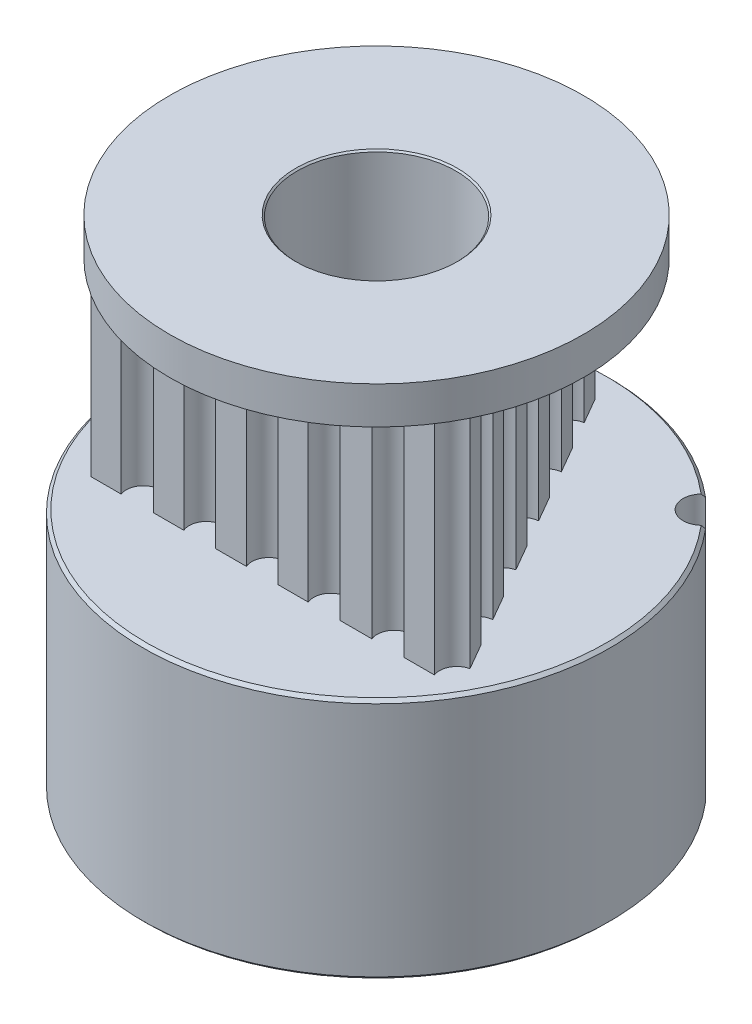
SolidWorks part; units mm, degrees
material "6061 slitina"
ref_plane "Přední rovina" through (0, 0, 0) normal (0, 0, 1) x (1, 0, 0)
ref_plane "Horní rovina" through (0, 0, 0) normal (0, 1, 0) x (1, 0, 0)
ref_plane "Pravá rovina" through (0, 0, 0) normal (1, 0, 0) x (0, 0, -1)
sketch "Skica1" plane through (0, 0, 0) normal (0, 1, 0) x (1, 0, 0)
  circle A0 centre (0, 0) radius 2.5
  arc B0 (-5.7301, 1.0983) -> (-5.3872, 2.2403) centre (-5.6803, 1.7058) ccw
  arc B1 (-5.7301, 1.0983) -> (-5.922, 1.0859) centre (-5.7841, 0.4401) ccw
  arc B2 (-5.922, 1.0859) -> (-6.0197, 1.0387) centre (-5.8743, 0.8624) ccw
  arc B3 (-6.0197, 1.0387) -> (-6.0791, 0.6004) centre (0, 0) ccw
  arc B4 (-6.0791, 0.6004) -> (-5.9974, 0.5289) centre (-5.892, 0.7317) ccw
  arc B5 (-5.9974, 0.5289) -> (-5.8158, 0.466) centre (-5.6927, 1.1148) ccw
  arc B6 (-5.7891, -0.7262) -> (-5.8158, 0.466) centre (-5.9294, -0.133) ccw
  arc B7 (-5.7891, -0.7262) -> (-5.9677, -0.7972) centre (-5.637, -1.3689) ccw
  arc B8 (-5.9677, -0.7972) -> (-6.0461, -0.8723) centre (-5.8532, -0.9951) ccw
  arc B9 (-6.0461, -0.8723) -> (-5.9671, -1.3075) centre (0, 0) ccw
  arc B10 (-5.9671, -1.3075) -> (-5.8673, -1.3503) centre (-5.8297, -1.1248) ccw
  arc B11 (-5.8673, -1.3503) -> (-5.6751, -1.354) centre (-5.7586, -0.6989) ccw
  arc B12 (-5.2813, -2.4796) -> (-5.6751, -1.354) centre (-5.5981, -1.9587) ccw
  arc B13 (-5.2813, -2.4796) -> (-5.4293, -2.6023) centre (-4.9381, -3.0438) ccw
  arc B14 (-5.4293, -2.6023) -> (-5.4806, -2.698) centre (-5.2593, -2.7551) ccw
  arc B15 (-5.4806, -2.698) -> (-5.271, -3.0875) centre (0, 0) ccw
  arc B16 (-5.271, -3.0875) -> (-5.1629, -3.0973) centre (-5.1968, -2.8713) ccw
  arc B17 (-5.1629, -3.0973) -> (-4.979, -3.0415) centre (-5.2608, -2.4442) ccw
  arc B18 (-4.2566, -3.9902) -> (-4.979, -3.0415) centre (-4.7188, -3.5928) ccw
  arc B19 (-4.2566, -3.9902) -> (-4.3594, -4.1527) centre (-3.7559, -4.4208) ccw
  arc B20 (-4.3594, -4.1527) -> (-4.3786, -4.2595) centre (-4.1505, -4.2455) ccw
  arc B21 (-4.3786, -4.2595) -> (-4.059, -4.5652) centre (0, 0) ccw
  arc B22 (-4.059, -4.5652) -> (-3.9531, -4.5412) centre (-4.0552, -4.3366) ccw
  arc B23 (-3.9531, -4.5412) -> (-3.7954, -4.4312) centre (-4.248, -3.9503) ccw
  arc B24 (-2.8152, -5.1103) -> (-3.7954, -4.4312) centre (-3.3776, -4.8751) ccw
  arc B25 (-2.8152, -5.1103) -> (-2.8628, -5.2965) centre (-2.2059, -5.3651) ccw
  arc B26 (-2.8628, -5.2965) -> (-2.8481, -5.4041) centre (-2.6354, -5.3203) ccw
  arc B27 (-2.8481, -5.4041) -> (-2.4496, -5.596) centre (0, 0) ccw
  arc B28 (-2.4496, -5.596) -> (-2.3563, -5.5405) centre (-2.5166, -5.3775) ccw
  arc B29 (-2.3563, -5.5405) -> (-2.2403, -5.3872) centre (-2.8194, -5.0696) ccw
  arc B30 (-1.0983, -5.7301) -> (-2.2403, -5.3872) centre (-1.7058, -5.6803) ccw
  arc B31 (-1.0983, -5.7301) -> (-1.0859, -5.922) centre (-0.4401, -5.7841) ccw
  arc B32 (-1.0859, -5.922) -> (-1.0387, -6.0197) centre (-0.8624, -5.8743) ccw
  arc B33 (-1.0387, -6.0197) -> (-0.6004, -6.0791) centre (0, 0) ccw
  arc B34 (-0.6004, -6.0791) -> (-0.5289, -5.9974) centre (-0.7317, -5.892) ccw
  arc B35 (-0.5289, -5.9974) -> (-0.466, -5.8158) centre (-1.1148, -5.6927) ccw
  arc B36 (0.7262, -5.7891) -> (-0.466, -5.8158) centre (0.133, -5.9294) ccw
  arc B37 (0.7262, -5.7891) -> (0.7972, -5.9677) centre (1.3689, -5.637) ccw
  arc B38 (0.7972, -5.9677) -> (0.8723, -6.0461) centre (0.9951, -5.8532) ccw
  arc B39 (0.8723, -6.0461) -> (1.3075, -5.9671) centre (0, 0) ccw
  arc B40 (1.3075, -5.9671) -> (1.3503, -5.8673) centre (1.1248, -5.8297) ccw
  arc B41 (1.3503, -5.8673) -> (1.354, -5.6751) centre (0.6989, -5.7586) ccw
  arc B42 (2.4796, -5.2813) -> (1.354, -5.6751) centre (1.9587, -5.5981) ccw
  arc B43 (2.4796, -5.2813) -> (2.6023, -5.4293) centre (3.0438, -4.9381) ccw
  arc B44 (2.6023, -5.4293) -> (2.698, -5.4806) centre (2.7551, -5.2593) ccw
  arc B45 (2.698, -5.4806) -> (3.0875, -5.271) centre (0, 0) ccw
  arc B46 (3.0875, -5.271) -> (3.0973, -5.1629) centre (2.8713, -5.1968) ccw
  arc B47 (3.0973, -5.1629) -> (3.0415, -4.979) centre (2.4442, -5.2608) ccw
  arc B48 (3.9902, -4.2566) -> (3.0415, -4.979) centre (3.5928, -4.7188) ccw
  arc B49 (3.9902, -4.2566) -> (4.1527, -4.3594) centre (4.4208, -3.7559) ccw
  arc B50 (4.1527, -4.3594) -> (4.2595, -4.3786) centre (4.2455, -4.1505) ccw
  arc B51 (4.2595, -4.3786) -> (4.5652, -4.059) centre (0, 0) ccw
  arc B52 (4.5652, -4.059) -> (4.5412, -3.9531) centre (4.3366, -4.0552) ccw
  arc B53 (4.5412, -3.9531) -> (4.4312, -3.7954) centre (3.9503, -4.248) ccw
  arc B54 (5.1103, -2.8152) -> (4.4312, -3.7954) centre (4.8751, -3.3776) ccw
  arc B55 (5.1103, -2.8152) -> (5.2965, -2.8628) centre (5.3651, -2.2059) ccw
  arc B56 (5.2965, -2.8628) -> (5.4041, -2.8481) centre (5.3203, -2.6354) ccw
  arc B57 (5.4041, -2.8481) -> (5.596, -2.4496) centre (0, 0) ccw
  arc B58 (5.596, -2.4496) -> (5.5405, -2.3563) centre (5.3775, -2.5166) ccw
  arc B59 (5.5405, -2.3563) -> (5.3872, -2.2403) centre (5.0696, -2.8194) ccw
  arc B60 (5.7301, -1.0983) -> (5.3872, -2.2403) centre (5.6803, -1.7058) ccw
  arc B61 (5.7301, -1.0983) -> (5.922, -1.0859) centre (5.7841, -0.4401) ccw
  arc B62 (5.922, -1.0859) -> (6.0197, -1.0387) centre (5.8743, -0.8624) ccw
  arc B63 (6.0197, -1.0387) -> (6.0791, -0.6004) centre (0, 0) ccw
  arc B64 (6.0791, -0.6004) -> (5.9974, -0.5289) centre (5.892, -0.7317) ccw
  arc B65 (5.9974, -0.5289) -> (5.8158, -0.466) centre (5.6927, -1.1148) ccw
  arc B66 (5.7891, 0.7262) -> (5.8158, -0.466) centre (5.9294, 0.133) ccw
  arc B67 (5.7891, 0.7262) -> (5.9677, 0.7972) centre (5.637, 1.3689) ccw
  arc B68 (5.9677, 0.7972) -> (6.0461, 0.8723) centre (5.8532, 0.9951) ccw
  arc B69 (6.0461, 0.8723) -> (5.9671, 1.3075) centre (0, 0) ccw
  arc B70 (5.9671, 1.3075) -> (5.8673, 1.3503) centre (5.8297, 1.1248) ccw
  arc B71 (5.8673, 1.3503) -> (5.6751, 1.354) centre (5.7586, 0.6989) ccw
  arc B72 (5.2813, 2.4796) -> (5.6751, 1.354) centre (5.5981, 1.9587) ccw
  arc B73 (5.2813, 2.4796) -> (5.4293, 2.6023) centre (4.9381, 3.0438) ccw
  arc B74 (5.4293, 2.6023) -> (5.4806, 2.698) centre (5.2593, 2.7551) ccw
  arc B75 (5.4806, 2.698) -> (5.271, 3.0875) centre (0, 0) ccw
  arc B76 (5.271, 3.0875) -> (5.1629, 3.0973) centre (5.1968, 2.8713) ccw
  arc B77 (5.1629, 3.0973) -> (4.979, 3.0415) centre (5.2608, 2.4442) ccw
  arc B78 (4.2566, 3.9902) -> (4.979, 3.0415) centre (4.7188, 3.5928) ccw
  arc B79 (4.2566, 3.9902) -> (4.3594, 4.1527) centre (3.7559, 4.4208) ccw
  arc B80 (4.3594, 4.1527) -> (4.3786, 4.2595) centre (4.1505, 4.2455) ccw
  arc B81 (4.3786, 4.2595) -> (4.059, 4.5652) centre (0, 0) ccw
  arc B82 (4.059, 4.5652) -> (3.9531, 4.5412) centre (4.0552, 4.3366) ccw
  arc B83 (3.9531, 4.5412) -> (3.7954, 4.4312) centre (4.248, 3.9503) ccw
  arc B84 (2.8152, 5.1103) -> (3.7954, 4.4312) centre (3.3776, 4.8751) ccw
  arc B85 (2.8152, 5.1103) -> (2.8628, 5.2965) centre (2.2059, 5.3651) ccw
  arc B86 (2.8628, 5.2965) -> (2.8481, 5.4041) centre (2.6354, 5.3203) ccw
  arc B87 (2.8481, 5.4041) -> (2.4496, 5.596) centre (0, 0) ccw
  arc B88 (2.4496, 5.596) -> (2.3563, 5.5405) centre (2.5166, 5.3775) ccw
  arc B89 (2.3563, 5.5405) -> (2.2403, 5.3872) centre (2.8194, 5.0696) ccw
  arc B90 (1.0983, 5.7301) -> (2.2403, 5.3872) centre (1.7058, 5.6803) ccw
  arc B91 (1.0983, 5.7301) -> (1.0859, 5.922) centre (0.4401, 5.7841) ccw
  arc B92 (1.0859, 5.922) -> (1.0387, 6.0197) centre (0.8624, 5.8743) ccw
  arc B93 (1.0387, 6.0197) -> (0.6004, 6.0791) centre (0, 0) ccw
  arc B94 (0.6004, 6.0791) -> (0.5289, 5.9974) centre (0.7317, 5.892) ccw
  arc B95 (0.5289, 5.9974) -> (0.466, 5.8158) centre (1.1148, 5.6927) ccw
  arc B96 (-0.7262, 5.7891) -> (0.466, 5.8158) centre (-0.133, 5.9294) ccw
  arc B97 (-0.7262, 5.7891) -> (-0.7972, 5.9677) centre (-1.3689, 5.637) ccw
  arc B98 (-0.7972, 5.9677) -> (-0.8723, 6.0461) centre (-0.9951, 5.8532) ccw
  arc B99 (-0.8723, 6.0461) -> (-1.3075, 5.9671) centre (0, 0) ccw
  arc B100 (-1.3075, 5.9671) -> (-1.3503, 5.8673) centre (-1.1248, 5.8297) ccw
  arc B101 (-1.3503, 5.8673) -> (-1.354, 5.6751) centre (-0.6989, 5.7586) ccw
  arc B102 (-2.4796, 5.2813) -> (-1.354, 5.6751) centre (-1.9587, 5.5981) ccw
  arc B103 (-2.4796, 5.2813) -> (-2.6023, 5.4293) centre (-3.0438, 4.9381) ccw
  arc B104 (-2.6023, 5.4293) -> (-2.698, 5.4806) centre (-2.7551, 5.2593) ccw
  arc B105 (-2.698, 5.4806) -> (-3.0875, 5.271) centre (0, 0) ccw
  arc B106 (-3.0875, 5.271) -> (-3.0973, 5.1629) centre (-2.8713, 5.1968) ccw
  arc B107 (-3.0973, 5.1629) -> (-3.0415, 4.979) centre (-2.4442, 5.2608) ccw
  arc B108 (-3.9902, 4.2566) -> (-3.0415, 4.979) centre (-3.5928, 4.7188) ccw
  arc B109 (-3.9902, 4.2566) -> (-4.1527, 4.3594) centre (-4.4208, 3.7559) ccw
  arc B110 (-4.1527, 4.3594) -> (-4.2595, 4.3786) centre (-4.2455, 4.1505) ccw
  arc B111 (-4.2595, 4.3786) -> (-4.5652, 4.059) centre (0, 0) ccw
  arc B112 (-4.5652, 4.059) -> (-4.5412, 3.9531) centre (-4.3366, 4.0552) ccw
  arc B113 (-4.5412, 3.9531) -> (-4.4312, 3.7954) centre (-3.9503, 4.248) ccw
  arc B114 (-5.1103, 2.8152) -> (-4.4312, 3.7954) centre (-4.8751, 3.3776) ccw
  arc B115 (-5.1103, 2.8152) -> (-5.2965, 2.8628) centre (-5.3651, 2.2059) ccw
  arc B116 (-5.2965, 2.8628) -> (-5.4041, 2.8481) centre (-5.3203, 2.6354) ccw
  arc B117 (-5.4041, 2.8481) -> (-5.596, 2.4496) centre (0, 0) ccw
  arc B118 (-5.596, 2.4496) -> (-5.5405, 2.3563) centre (-5.3775, 2.5166) ccw
  arc B119 (-5.5405, 2.3563) -> (-5.3872, 2.2403) centre (-5.0696, 2.8194) ccw
  dimension "D1" = 5
sketch_block_instance "Blok1-1"
sketch_block "Blok1"
extrude "Přidat vysunutím1" add sketch "Skica1" along normal blind 7 from offset 7.8
sketch "Skica2" plane through (0, 7.8, 0) normal (0, -1, 0) x (1, 0, 0)
  circle A0 centre (0, 0) radius 3.5
  circle A1 centre (0, 0) radius 2.5 construction
  circle A2 centre (0, 0) radius 2.5
  dimension "D1" = 7
extrude "Přidat vysunutím2" add sketch "Skica2" along normal blind 7.8
sketch "Skica3" plane through (0, 14.8, 0) normal (0, 1, 0) x (1, 0, 0)
  circle A0 centre (0, 0) radius 3.5
  circle A1 centre (0, 0) radius 2.5 construction
  circle A2 centre (0, 0) radius 2.5
  dimension "D1" = 7
extrude "Přidat vysunutím3" add sketch "Skica3" along normal blind 1.2
sketch "Skica5" plane through (0, 16, 0) normal (0, 1, 0) x (1, 0, 0)
  circle A0 centre (0, 0) radius 7.5
  circle A3 centre (0, 0) radius 3.5 construction
  circle A4 centre (0, 0) radius 3.5
  dimension "D1" = 15
extrude "Přidat vysunutím4" add sketch "Skica5" against normal up to surface (1.2 mm away) separate body up to face at (0, 14.8, 0)
sketch "Skica6" plane through (0, 0, 0) normal (0, -1, 0) x (1, 0, 0)
  circle A0 centre (0, 0) radius 7.5
  circle A1 centre (0, 0) radius 3.5 construction
  circle A2 centre (0, 0) radius 3.5
  circle A3 centre (0, 0) radius 7.5 construction
extrude "Přidat vysunutím5" add sketch "Skica6" against normal up to surface (7.8 mm away) separate body up to face at (0, 7.8, 0)
chamfer "Zkosení1" distance 0.1 angle 45 2 edges at (0, 14.8, 7.5) (0, 16, 7.5)
chamfer "Zkosení2" distance 0.1 angle 45 2 edges at (0, 0, -2.5) (0, 16, 2.5)
chamfer "Zkosení3" distance 0.1 angle 45 2 edges at (0, 0, -7.5) (0, 7.8, 7.5)
sketch "Sketch8" plane through (0, 16, 0) normal (0, 1, 0) x (1, 0, 0)
  circle A0 centre (0, 0) radius 6.65
extrude "Cut-Extrude2" cut sketch "Sketch8" against normal blind 5 flip side to cut contours A0
ref_plane "Plane1" through (0, 0, -7.5) normal (0, 0, -1) x (-1, 0, 0)
ref_plane "Plane2" through (-7.5, 0, 0) normal (-1, 0, 0) x (0, 0, 1)
sketch "Sketch20" plane through (-7.5, 0, 0) normal (-1, 0, 0) x (0, 0, 1)
  line L0 (0, 0.1) -> (0, 7.7)
  line L1 (-7.5, 0.1) -> (7.5, 0.1) construction
  line L2 (7.5, 7.7) -> (-7.5, 7.7) construction
  circle A0 centre (0, 3.9) radius 1.5
sketch "Sketch25" plane through (0, 7.8, 0) normal (0, 1, 0) x (1, 0, 0)
  line L0 (-0.7179, 6.0965) -> (-0.9071, 5.7689)
  line L5 (-5.5084, -3.67) -> (-4.5368, -3.67)
  line L6 (5.926, -2.9242) -> (5.4338, -2.0716)
  line L9 (-5.4363, -2.0759) -> (-5.8989, -2.8773)
  line L23 (-3.4987, -3.67) -> (-2.5208, -3.67)
  line L24 (-4.4422, -0.3541) -> (-4.912, -1.1678)
  line L26 (-1.4992, -3.67) -> (-0.513, -3.67)
  line L27 (2.4958, -3.67) -> (3.5189, -3.67)
  line L28 (4.926, -1.192) -> (4.4459, -0.3606)
  line L29 (4.549, -3.67) -> (5.5306, -3.67)
  line L30 (0.5086, -3.67) -> (1.4742, -3.67)
  line L31 (3.9112, 0.5657) -> (3.4185, 1.419)
  line L32 (1.9163, 4.0209) -> (1.4364, 4.8521)
  line L33 (-1.4233, 4.8748) -> (-1.9185, 4.0171)
  line L34 (2.9152, 2.2908) -> (2.4274, 3.1357)
  line L35 (0.9141, 5.7568) -> (0.4321, 6.5916)
  line L37 (-2.4409, 3.1122) -> (-2.9162, 2.2891)
  line L39 (-0.7179, 6.0965) -> (-0.4321, 6.5916)
  line L40 (-3.4352, 1.3901) -> (-3.9277, 0.5371)
  line L42 (-0.4321, 6.5916) -> (-0.9071, 5.7689) [skipped]
  arc A24 (-0.4321, 6.5916) -> (0.4321, 6.5916) centre (0, 6.94) ccw
  arc A25 (-1.4233, 4.8748) -> (-0.9071, 5.7689) centre (-0.9887, 5.22) ccw
  arc A26 (-2.4409, 3.1122) -> (-1.9185, 4.0171) centre (-2.0176, 3.471) ccw
  arc A27 (0.9141, 5.7568) -> (1.4364, 4.8521) centre (1.0128, 5.2106) ccw
  arc A28 (1.9163, 4.0209) -> (2.4274, 3.1357) centre (1.9844, 3.4701) ccw
  arc A29 (-3.4352, 1.3901) -> (-2.9162, 2.2891) centre (-3.0054, 1.7413) ccw
  arc A30 (-4.4422, -0.3541) -> (-3.9277, 0.5371) centre (-4.0048, -0.0125) ccw
  arc A31 (-5.4363, -2.0759) -> (-4.912, -1.1678) centre (-5.0165, -1.7129) ccw
  arc A32 (-5.5084, -3.67) -> (-5.8989, -2.8773) centre (-6.0049, -3.4221) ccw
  arc A33 (-3.4987, -3.67) -> (-4.5368, -3.67) centre (-4.0177, -3.4735) ccw
  arc A34 (-1.4992, -3.67) -> (-2.5208, -3.67) centre (-2.01, -3.4529) ccw
  arc A35 (0.5086, -3.67) -> (-0.513, -3.67) centre (-0.0022, -3.4529) ccw
  arc A36 (2.4958, -3.67) -> (1.4742, -3.67) centre (1.985, -3.4529) ccw
  arc A37 (4.549, -3.67) -> (3.5189, -3.67) centre (4.0339, -3.4632) ccw
  arc A38 (2.9152, 2.2908) -> (3.4185, 1.419) centre (2.9643, 1.738) ccw
  arc A39 (3.9112, 0.5657) -> (4.4459, -0.3606) centre (4.05, 0.0283) ccw
  arc A40 (4.926, -1.192) -> (5.4338, -2.0716) centre (4.9859, -1.7438) ccw
  arc A41 (5.926, -2.9242) -> (5.5306, -3.67) centre (6.0467, -3.4659) ccw
  point P0 (-1.0017, 5.205)
  point P6 (-2.0034, 3.47)
  point P7 (-3.0051, 1.735)
  point P9 (-4.0068, 0)
  point P10 (-5.0085, -1.735)
  point P11 (5.0085, -1.735)
  point P12 (4.0068, 0)
  point P13 (3.0051, 1.735)
  point P14 (2.0034, 3.47)
  point P15 (1.0017, 5.205)
  point P16 (-4.0068, -3.47)
  point P20 (-2.0034, -3.47)
  point P21 (0, -3.47)
  point P23 (2.0034, -3.47)
  point P24 (4.0068, -3.47)
sketch "Sketch30" plane through (0, 0, 0) normal (0, -1, 0) x (1, 0, 0)
  line L0 (0, 0) -> (6.782, 0)
  line L1 (6.782, 0) -> (0, -6.782)
  line L2 (-0.1186, 0) -> (3.391, -3.391)
  line L3 (3.391, -3.391) -> (4.7956, -4.7956)
  line L4 (4.7956, -4.7956) -> (5.2326, -5.2326)
  circle A0 centre (0, 0) radius 6.782
  circle A1 centre (0, 0) radius 7.4 construction
  circle A2 centre (5.2326, -5.2326) radius 0.618
sketch "Sketch31" plane through (0, 0, 0) normal (0, -1, 0) x (1, 0, 0)
  circle A1 centre (0, 0) radius 2.55
sketch "Sketch19" plane through (0, 0, -7.5) normal (0, 0, -1) x (-1, 0, 0)
  line L0 (0, 0.1) -> (0, 7.7)
  line L1 (7.5, 0.1) -> (-7.5, 0.1) construction
  line L2 (-7.5, 7.7) -> (7.5, 7.7) construction
  circle A0 centre (0, 3.9) radius 1.5
sketch "Sketch32" plane through (0, 7.8, 0) normal (0, 1, 0) x (1, 0, 0)
  circle A0 centre (0, 0) radius 6.65
extrude "Cut-Extrude3" cut sketch "Sketch32" along normal blind 7
extrude "Boss-Extrude1" add sketch "Sketch25" along normal blind 7
sketch "Sketch34" plane through (0, 16, 0) normal (0, 1, 0) x (1, 0, 0)
  circle A0 centre (0, 0) radius 2.55
extrude "Cut-Extrude4" cut sketch "Sketch34" against normal blind 30
extrude "Cut-Extrude5" cut sketch "Sketch20" against normal blind 8 contours A0
extrude "Cut-Extrude6" cut sketch "Sketch19" against normal blind 8 contours A0
extrude "Cut-Extrude7" cut sketch "Sketch30" against normal blind 8 contours A2
